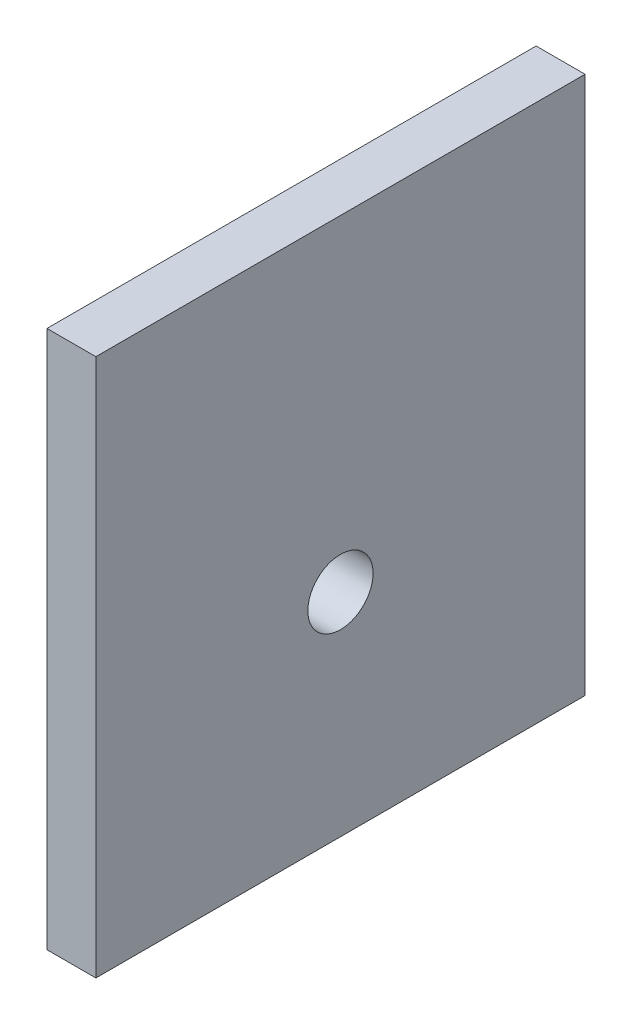
SolidWorks part; units mm, degrees
ref_plane "Front" through (0, 0, 0) normal (0, 0, 1) x (1, 0, 0)
ref_plane "Top" through (0, 0, 0) normal (0, 1, 0) x (1, 0, 0)
ref_plane "Right" through (0, 0, 0) normal (1, 0, 0) x (0, 0, -1)
sketch "草图1" plane through (0, 0, 0) normal (1, 0, 0) x (0, 0, -1)
  line L1 (15, -20) -> (-15, -20)
  line L2 (15, -20) -> (15, 20)
  line L3 (15, 20) -> (-15, 20)
  line L4 (-15, -20) -> (-15, 20)
  line L5 (15, -20) -> (-15, 20) construction
  line L6 (15, 20) -> (-15, -20) construction
  point P0 (0, 0)
  dimension "D1" = 30
  dimension "D2" = 40
extrude "凸台-拉伸1" add sketch "草图1" along normal blind 3
sketch "草图2" plane through (3, 0, 0) normal (1, 0, 0) x (0, 0, -1)
  circle A0 centre (0, 0) radius 2
  dimension "D1" = 4
extrude "切除-拉伸1" cut sketch "草图2" against normal through all
sketch "草图3" plane through (0, 0, 0) normal (-1, 0, 0) x (0, 0, 1)
  line L0 (-15, -20) -> (-15, 20) construction
  line L1 (15, -20) -> (-15, -20)
  line L2 (15, -20) -> (15, -13)
  line L3 (15, -13) -> (-15, -13)
  line L4 (-15, -20) -> (-15, -13)
  dimension "D1" = 7
extrude "切除-拉伸2" cut sketch "草图3" against normal through all
